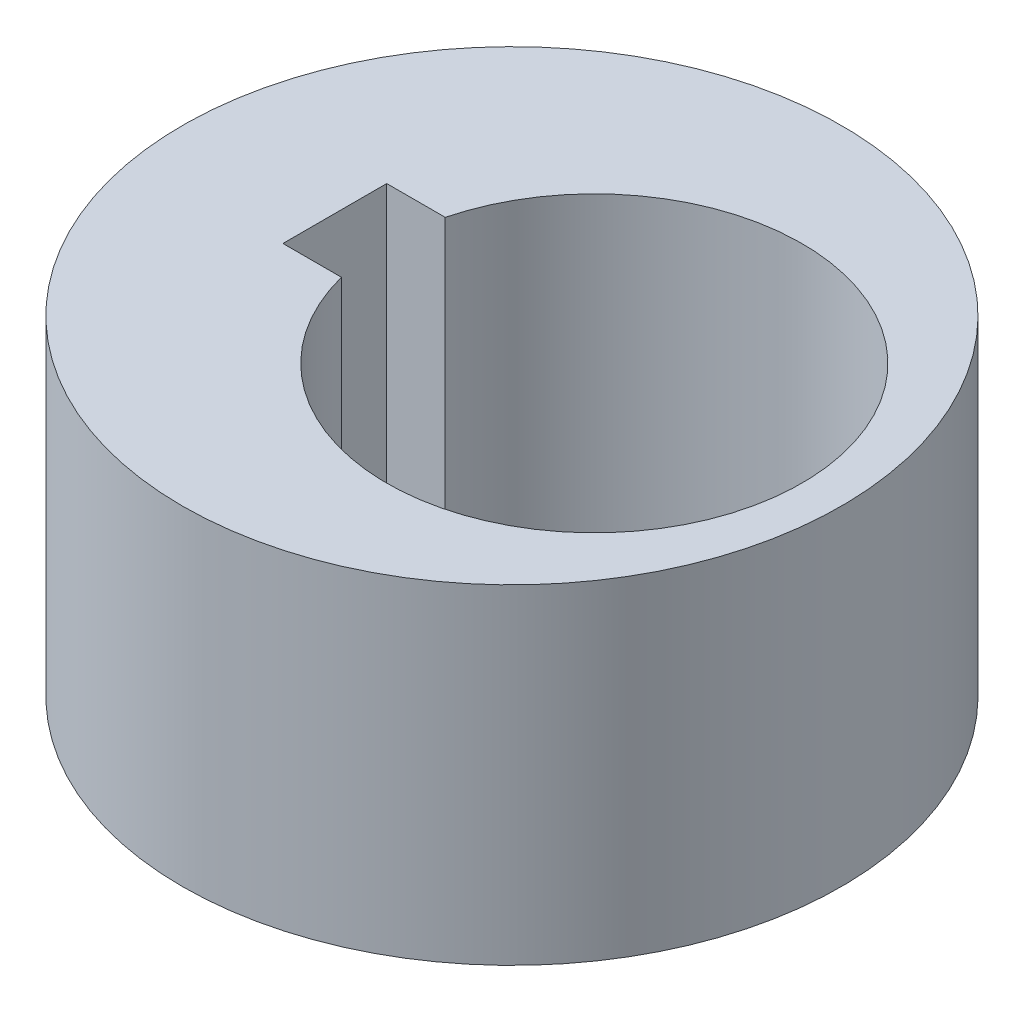
SolidWorks part; units mm, degrees
material "6061-T6 (SS)"
ref_plane "Front Plane" through (0, 0, 0) normal (0, 0, 1) x (1, 0, 0)
ref_plane "Top Plane" through (0, 0, 0) normal (0, 1, 0) x (1, 0, 0)
ref_plane "Right Plane" through (0, 0, 0) normal (1, 0, 0) x (0, 0, -1)
sketch "Sketch1" plane through (0, 0, 0) normal (0, 1, 0) x (1, 0, 0)
  circle A0 centre (0, 0) radius 6.35
  dimension "D1" = 12.7
extrude "Boss-Extrude1" add sketch "Sketch1" along normal blind 6.35
sketch "Sketch2" plane through (0, 6.35, 0) normal (0, 1, 0) x (1, 0, 0)
  line L0 (0, 0) -> (1.5875, 0) construction
  circle A0 centre (1.5875, 0) radius 4
  dimension "D2" = 8
  dimension "D1" = 1.5875
extrude "Cut-Extrude1" cut sketch "Sketch2" against normal blind 6.35
sketch "Sketch3" plane through (0, 6.35, 0) normal (0, 1, 0) x (1, 0, 0)
  line L0 (-2.4125, 0) -> (0, 0) construction
  line L1 (-3.4125, -1) -> (-1.4125, -1)
  line L2 (-3.4125, -1) -> (-3.4125, 1)
  line L3 (-3.4125, 1) -> (-1.4125, 1)
  line L4 (-1.4125, -1) -> (-1.4125, 1)
  line L5 (-3.4125, -1) -> (-1.4125, 1) construction
  line L6 (-3.4125, 1) -> (-1.4125, -1) construction
  circle A0 centre (1.5875, 0) radius 4 construction
  point P0 (-2.4125, 0)
  dimension "D1" = 2
  dimension "D2" = 2
extrude "Cut-Extrude2" cut sketch "Sketch3" against normal blind 6.35
